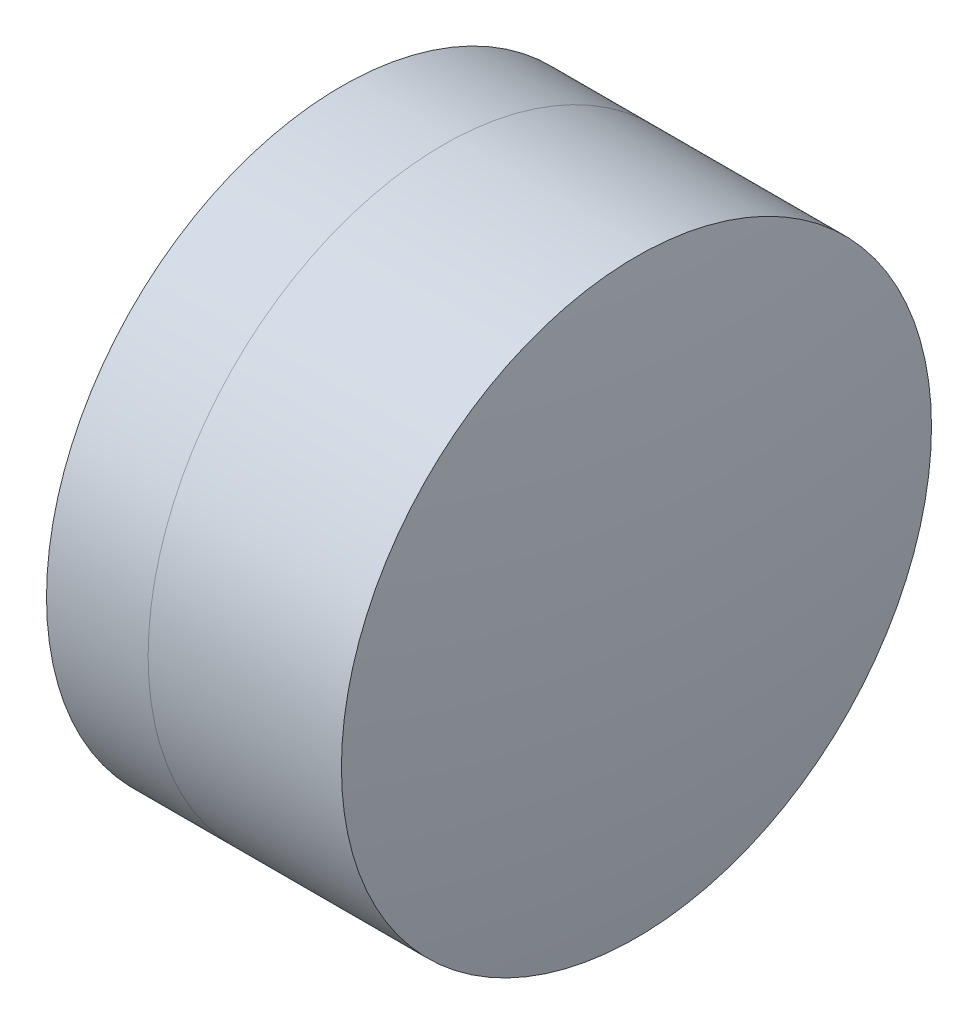
SolidWorks part; units mm, degrees
ref_plane "前视基准面" through (0, 0, 0) normal (0, 0, 1) x (1, 0, 0)
ref_plane "上视基准面" through (0, 0, 0) normal (0, 1, 0) x (1, 0, 0)
ref_plane "右视基准面" through (0, 0, 0) normal (1, 0, 0) x (0, 0, -1)
sketch "草图1" plane through (0, 0, 0) normal (0, 1, 0) x (1, 0, 0)
  line L0 (-9.7026, 0) -> (11.7646, 0) construction
  line L1 (-0.3598, -3.175) -> (0.7336, -3.175)
  line L2 (-0.3598, 3.175) -> (0.7336, 3.175)
  arc A0 (0.7336, -3.175) -> (0.7336, 3.175) centre (-5.0526, 0) ccw
  arc A1 (-0.3598, 3.175) -> (-0.3598, -3.175) centre (7.8474, 0) ccw
  point P10 (-0.9526, 0)
  point P11 (1.5474, 0)
  dimension "D3" = 8.8
  dimension "D4" = 6.6
  dimension "D1" = 3.175
  dimension "D2" = 3.175
  dimension "D5" = 2.5
revolve "旋转1" add sketch "草图1" angle 360 about L0
sketch "草图2" plane through (0, 0, 0) normal (0, 1, 0) x (1, 0, 0)
  line L0 (-0.5519, 0) -> (13.3053, 0) construction
  line L2 (0.7336, 3.175) -> (2.8139, 3.175)
  line L3 (0.7336, -3.175) -> (2.8139, -3.175)
  arc A0 (2.8139, -3.175) -> (2.8139, 3.175) centre (-18.6526, 0) ccw
  arc A1 (0.7336, -3.175) -> (0.7336, 3.175) centre (-5.0526, 0) ccw construction
  arc A2 (0.7336, -3.175) -> (0.7336, 3.175) centre (-5.0526, 0) ccw
  point P4 (1.5474, 0)
  point P8 (3.0474, 0)
  dimension "D1" = 21.7
  dimension "D2" = 1.5
revolve "旋转3" add sketch "草图2" angle 360 about L0
